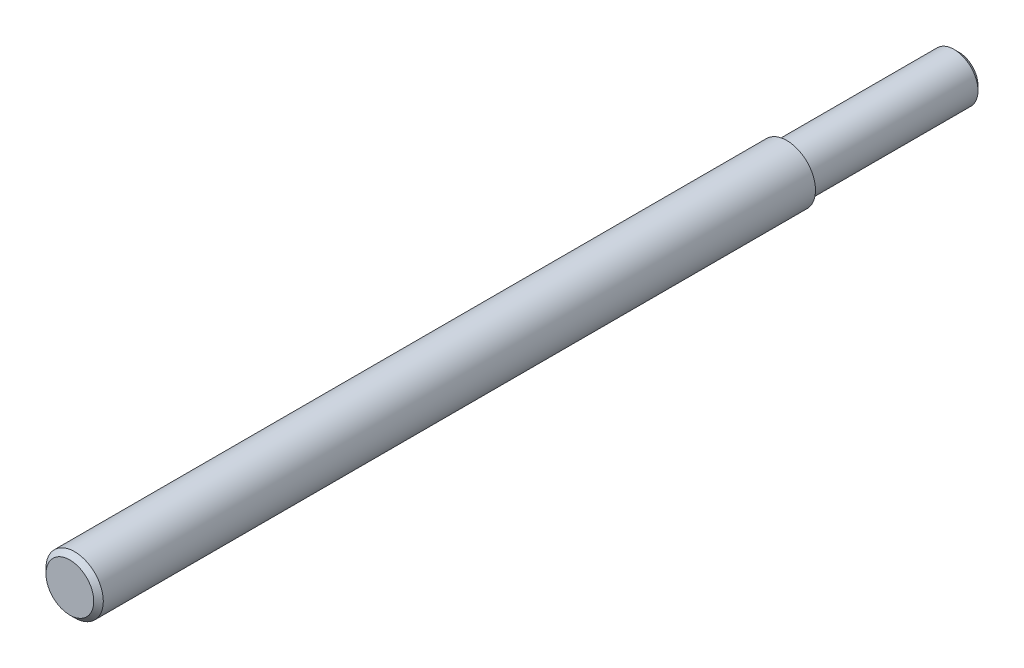
SolidWorks part; units mm, degrees
ref_plane "Front Plane" through (0, 0, 0) normal (0, 0, 1) x (1, 0, 0)
ref_plane "Top Plane" through (0, 0, 0) normal (0, 1, 0) x (1, 0, 0)
ref_plane "Right Plane" through (0, 0, 0) normal (1, 0, 0) x (0, 0, -1)
sketch "Sketch1" plane through (0, 0, 0) normal (0, 0, 1) x (1, 0, 0)
  circle A0 centre (0, 0) radius 5
  dimension "D1" = 10
extrude "Boss-Extrude1" add sketch "Sketch1" along normal blind 36
sketch "Sketch2" plane through (0, 0, 36) normal (0, 0, 1) x (1, 0, 0)
  circle A0 centre (0, 0) radius 6
  dimension "D1" = 12
extrude "Boss-Extrude2" add sketch "Sketch2" along normal blind 150
chamfer "Chamfer1" distance 1 angle 45 2 edges at (6, 0, 186) (5, 0, 0)
